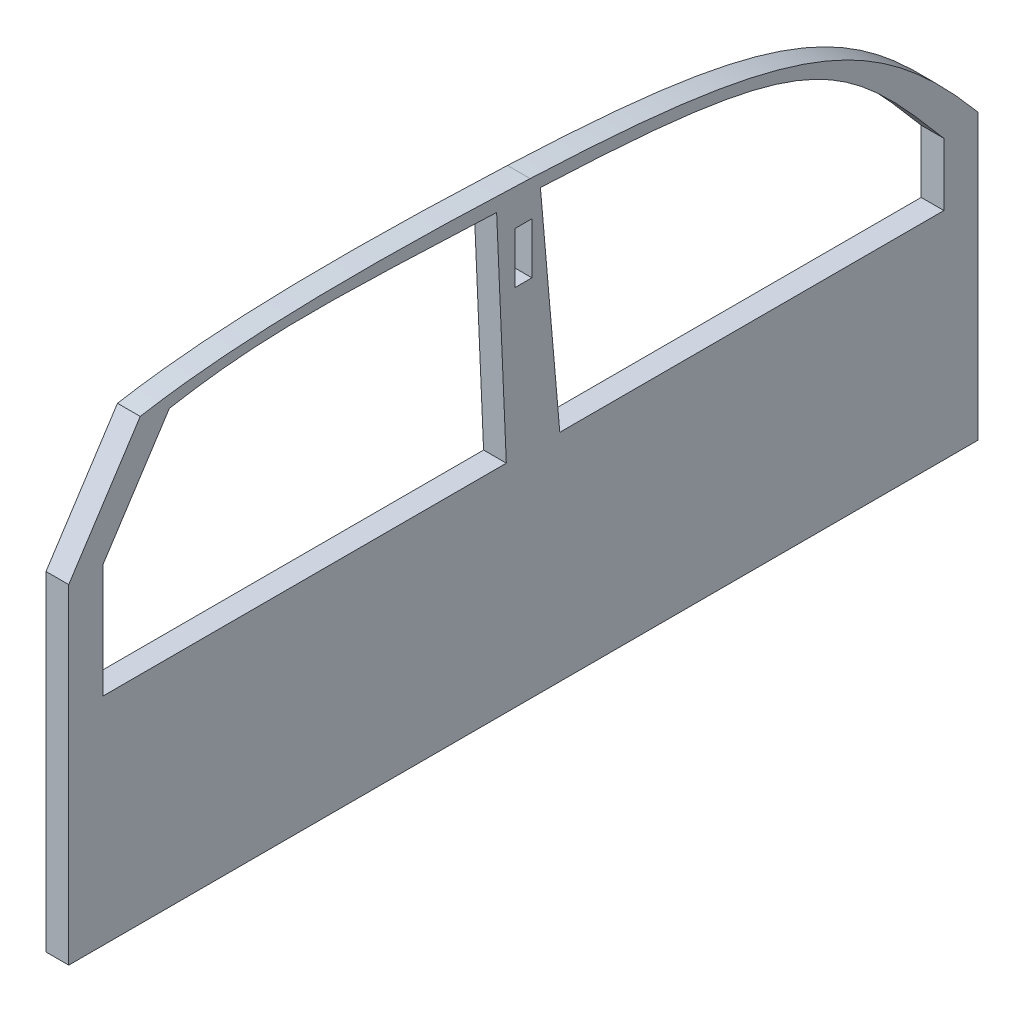
SolidWorks part; units mm, degrees
ref_plane "정면" through (0, 0, 0) normal (0, 0, 1) x (1, 0, 0)
ref_plane "윗면" through (0, 0, 0) normal (0, 1, 0) x (1, 0, 0)
ref_plane "우측면" through (0, 0, 0) normal (1, 0, 0) x (0, 0, -1)
sketch "스케치1" plane through (0, 0, 0) normal (1, 0, 0) x (0, 0, -1)
  line L0 (-3.3731, 1.3955) -> (806.6253, -0.2335) construction
  line L3 (-16.8598, -262.5989) -> (783.1402, -262.5989)
  line L4 (783.1402, -262.5989) -> (783.1402, -12.5989)
  line L5 (46.037, 124.0968) -> (-16.8598, 27.4011)
  line L6 (-16.8598, 27.4011) -> (-16.8598, -262.5989)
  line L7 (71.6817, 117.4011) -> (13.1402, 27.4011)
  line L8 (13.1402, 27.4011) -> (13.1402, -72.5989)
  line L9 (753.1402, -72.5989) -> (415.2005, -72.5989)
  line L10 (359.6137, 122.6887) -> (368.1402, -72.5989)
  line L11 (398.1402, 122.4011) -> (415.2005, -72.5989)
  line L12 (753.1402, -72.5989) -> (753.1402, -17.5989)
  line L13 (368.1402, -72.5989) -> (13.1402, -72.5989)
  line L14 (721.9329, 137.4011) -> (-160.4171, 137.4011) construction
  line L15 (-483.5029, 127.9567) -> (583.3662, 127.9567) construction
  line L16 (390.6402, 102.4011) -> (375.6402, 102.4011)
  line L17 (390.6402, 102.4011) -> (390.6402, 57.4011)
  line L18 (390.6402, 57.4011) -> (375.6402, 57.4011)
  line L19 (375.6402, 102.4011) -> (375.6402, 57.4011)
  line L21 (481.5005, 346.8813) -> (1084.7799, -372.0792) construction
  line L22 (1020.0401, -335.6779) -> (486.2403, 300.48) construction
  line L23 (383.1402, -262.5989) -> (-16.8598, -262.5989) construction
  line L24 (783.1402, -262.5989) -> (383.1402, -262.5989) construction
  line L25 (783.1402, -262.5989) -> (783.1402, 137.4011) construction
  line L26 (783.1402, 137.4011) -> (383.1402, 137.4011) construction
  line L27 (383.1402, -262.5989) -> (383.1402, 137.4011) construction
  line L28 (383.1402, -262.5989) -> (383.1402, 137.4011) construction
  line L29 (383.1402, 137.4011) -> (-16.8598, 137.4011) construction
  line L30 (-16.8598, -262.5989) -> (-16.8598, 137.4011) construction
  line L31 (1117.7891, 90.9805) -> (-321.5087, 153.8216) construction
  line L32 (-274.6111, 162.7406) -> (1052.8381, 104.783) construction
  line L33 (658.129, 109.6553) -> (61.0985, 135.7222) construction
  line L34 (311.8694, 159.7526) -> (-168.506, 75.0495) construction
  line L35 (-195.1858, 81.5627) -> (290.6223, 167.2238) construction
  line L36 (-78.6516, 154.1849) -> (856.899, 113.3378) construction
  spline S0 degree 3 poles (783.1402, -12.5989) (693.1499, 94.6473) (622.2247, 123.5839) (389.1135, 133.7618) knots 0 0 0 0 1 1 1 1
  spline S1 degree 3 poles (389.1135, 133.7618) (239.2562, 140.3047) (128.1043, 138.5675) (46.037, 124.0968) knots 0 0 0 0 1 1 1 1
  spline S2 degree 3 poles (71.6817, 117.4011) (153.749, 131.8717) (209.7565, 129.2317) (359.6137, 122.6887) knots 0 0 0 0 0.860293 0.860293 0.860293 0.860293
  spline S3 degree 3 poles (398.1402, 122.4011) (631.2514, 112.2232) (663.1499, 89.6473) (753.1402, -17.5989) knots 0.027736 0.027736 0.027736 0.027736 0.84207 0.84207 0.84207 0.84207
  point P21 (753.1402, -72.5989)
  point P25 (383.1402, 102.4011)
  dimension "D7" = 800
  dimension "D12" = 400
  dimension "D10" = 15
  dimension "D14" = 30
  dimension "D17" = 40
  dimension "D19" = 40
  dimension "D20" = 95
  dimension "D27" = 87.5
  dimension "D28" = 87.5
  dimension "D29" = 92.5
  dimension "D30" = 100
  dimension "D31" = 100
  dimension "D32" = 420
  dimension "D33" = 420
  dimension "D34" = 700
  dimension "D35" = 700
  dimension "D36" = 87.5
  dimension "D37" = 450
  dimension "D38" = 450
  dimension "D39" = 250
  dimension "D40" = 250
  dimension "D1" = 810
  dimension "D2" = 355
  dimension "D3" = 195
  dimension "D4" = 190
  dimension "D5" = 355
  dimension "D6" = 190
  dimension "D8" = 30
  dimension "D9" = 55
  dimension "D11" = 45
  dimension "D13" = 15
  dimension "D15" = 250
  dimension "D16" = 290
  dimension "D18" = 100
  dimension "D21" = 87.5
  dimension "D22" = 400
  dimension "D23" = 400
  dimension "D24" = 400
  dimension "D25" = 400
  dimension "D26" = 320
extrude "보스-돌출1" add sketch "스케치1" along normal blind 20
